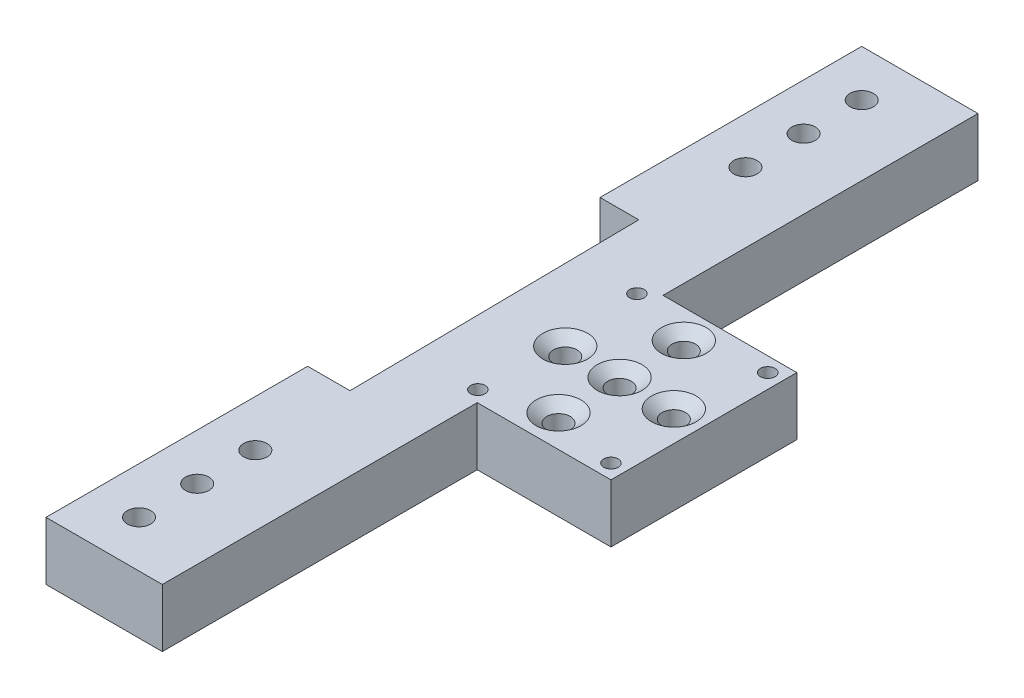
SolidWorks part; units mm, degrees
ref_plane "Front" through (0, 0, 0) normal (0, 0, 1) x (1, 0, 0)
ref_plane "Top" through (0, 0, 0) normal (0, 1, 0) x (1, 0, 0)
ref_plane "Right" through (0, 0, 0) normal (1, 0, 0) x (0, 0, -1)
sketch "Sketch1" plane through (0, 0, 0) normal (0, 1, 0) x (1, 0, 0)
  line L0 (24.6163, 0) -> (53.8263, 0)
  line L1 (53.8263, 0) -> (53.8263, 40.5892)
  line L2 (53.8263, 40.5892) -> (24.6163, 40.5892)
  line L3 (24.6163, 40.5892) -> (24.6163, 109.3724)
  line L4 (24.6163, 0) -> (24.6163, -68.7832)
  line L5 (24.6163, 109.3724) -> (-0.7837, 109.3724)
  line L6 (24.6163, -68.7832) -> (-0.7837, -68.7832)
  line L7 (-0.7837, 109.3724) -> (-0.7837, 52.2224)
  line L8 (-0.7837, -68.7832) -> (-0.7837, -11.6332)
  line L9 (-0.7837, -11.6332) -> (8.4582, -11.6332)
  line L10 (-0.7837, 52.2224) -> (7.6745, 52.2224)
  line L11 (7.6745, 52.2224) -> (8.4582, -11.6332)
extrude "Boss-Extrude1" add sketch "Sketch1" along normal blind 12.7
sketch "Sketch2" plane through (0, 12.7, 0) normal (0, 1, 0) x (1, 0, 0)
  line L0 (-0.7837, -68.7832) -> (-0.7837, -58.6232)
  line L1 (53.8263, 37.4142) -> (50.6513, 37.4142)
  line L2 (-0.7837, -11.6332) -> (-0.7837, -68.7832) construction
  line L3 (24.6163, 40.5892) -> (24.6163, 38.0492)
  line L4 (-0.7837, -58.6232) -> (9.3763, -58.6232)
  line L5 (-0.7837, 109.3724) -> (9.3763, 109.3724)
  line L6 (24.6163, 109.3724) -> (-0.7837, 109.3724) construction
  line L7 (9.3763, 109.3724) -> (9.3763, 99.2124)
  line L8 (53.8263, 20.2946) -> (35.4113, 20.2946)
  line L9 (53.8263, 0) -> (53.8263, 40.5892) construction
  line L10 (53.8263, 0) -> (53.8263, 3.175)
  line L11 (53.8263, 3.175) -> (50.6513, 3.175)
  line L12 (53.8263, 40.5892) -> (53.8263, 37.4142)
  line L13 (24.6163, 38.0492) -> (21.4413, 38.0492)
  line L14 (24.6163, 0) -> (24.6163, 2.54)
  line L15 (24.6163, 2.54) -> (22.2142, 2.54)
hole_wizard "1/4-20 Tapped Hole1" positions "Sketch11" profile "Sketch12" tap size "1/4-20" standard "ANSI Inch" end condition up to next
sketch "Sketch11" plane through (0, 12.7, 0) normal (0, 1, 0) x (1, 0, 0)
  point P0 (9.3763, 99.2124)
sketch "Sketch12" plane through (9.3763, 12.7, -99.2124) normal (1, 0, 0) x (0, 0, 1)
  line L0 (0, 0) -> (0, 12.7)
  line L1 (0, 12.7) -> (2.5527, 12.7)
  line L2 (2.5527, 12.7) -> (2.5527, 0)
  line L5 (2.5527, 0) -> (0, 0)
  line L11 (0, -6.35) -> (0, 107.95) construction
  dimension "Thread Major Dia." = 5.1054
  dimension "Thru Tap Drill Depth" = 12.7
hole_wizard "1/4-20 Tapped Hole2" positions "Sketch13" profile "Sketch14" tap size "1/4-20" standard "ANSI Inch" end condition up to next
sketch "Sketch13" plane through (0, 12.7, 0) normal (0, 1, 0) x (1, 0, 0)
  point P0 (9.3763, -58.6232)
sketch "Sketch14" plane through (9.3763, 12.7, 58.6232) normal (1, 0, 0) x (0, 0, 1)
  line L0 (0, 0) -> (0, 12.7)
  line L1 (0, 12.7) -> (2.5527, 12.7)
  line L2 (2.5527, 12.7) -> (2.5527, 0)
  line L5 (2.5527, 0) -> (0, 0)
  line L11 (0, -6.35) -> (0, 107.95) construction
  dimension "Thread Major Dia." = 5.1054
  dimension "Thru Tap Drill Depth" = 12.7
pattern_linear "LPattern1" count 3 spacing 12.7 along (0, 0, 1) of "1/4-20 Tapped Hole1"
pattern_linear "LPattern2" count 3 spacing 12.7 along (0, 0, -1) of "1/4-20 Tapped Hole2"
hole_wizard "CSK for #10 Flat Head Machine Screw (100)2" positions "Sketch20" profile "Sketch21" countersink size "#10" standard "ANSI Inch" end condition up to next
sketch "Sketch20" plane through (0, 12.7, 0) normal (0, 1, 0) x (1, 0, 0)
  point P0 (35.4113, 20.2946)
  point P3 (35.4113, 34.3262)
  point P5 (35.4113, 6.9607)
sketch "Sketch21" plane through (35.4113, 12.7, -20.2946) normal (1, 0, 0) x (0, 0, 1)
  line L0 (0, 0) -> (0, 12.7)
  line L1 (0, 12.7) -> (2.5527, 12.7)
  line L2 (2.5527, 12.7) -> (2.5527, 1.9608)
  line L3 (2.5527, 1.9608) -> (4.8895, 0)
  line L5 (4.8895, 0) -> (0, 0)
  line L6 (-2.5527, 1.9608) -> (-4.8895, 0) construction
  line L11 (0, -6.35) -> (0, 107.95) construction
  dimension "Thru Hole Dia." = 5.1054
  dimension "Thru Hole Depth" = 12.7
  dimension "Near C'Sink Dia." = 9.779
  dimension "Near C'Sink Angle" = 100
hole_wizard "1/8 (0.125) Diameter Hole1" positions "Sketch27" profile "Sketch28" hole size "1/8" standard "ANSI Inch" end condition up to next
sketch "Sketch27" plane through (0, 12.7, 0) normal (0, 1, 0) x (1, 0, 0)
  point P0 (21.4413, 38.0492)
  point P3 (22.2142, 2.54)
  point P6 (50.6513, 3.175)
  point P9 (50.6513, 37.4142)
sketch "Sketch28" plane through (21.4413, 12.7, -38.0492) normal (1, 0, 0) x (0, 0, 1)
  line L0 (0, 0) -> (0, 12.7)
  line L1 (0, 12.7) -> (1.5875, 12.7)
  line L2 (1.5875, 12.7) -> (1.5875, 0)
  line L5 (1.5875, 0) -> (0, 0)
  line L11 (0, -6.35) -> (0, 107.95) construction
  dimension "Thru Hole Dia." = 3.175
  dimension "Thru Hole Depth" = 12.7
hole_wizard "CSK for #10 Flat Head Machine Screw (100)3" positions "Sketch29" profile "Sketch30" countersink size "#10" standard "ANSI Inch" end condition up to next
sketch "Sketch29" plane through (0, 12.7, 0) normal (0, 1, 0) x (1, 0, 0)
  line L0 (53.8263, 20.2946) -> (35.4113, 20.2946) construction
  point P0 (47.2605, 20.2946)
  point P4 (23.5448, 20.2946)
sketch "Sketch30" plane through (47.2605, 12.7, -20.2946) normal (1, 0, 0) x (0, 0, 1)
  line L0 (0, 0) -> (0, 12.7)
  line L1 (0, 12.7) -> (2.5527, 12.7)
  line L2 (2.5527, 12.7) -> (2.5527, 1.9608)
  line L3 (2.5527, 1.9608) -> (4.8895, 0)
  line L5 (4.8895, 0) -> (0, 0)
  line L6 (-2.5527, 1.9608) -> (-4.8895, 0) construction
  line L11 (0, -6.35) -> (0, 107.95) construction
  dimension "Thru Hole Dia." = 5.1054
  dimension "Thru Hole Depth" = 12.7
  dimension "Near C'Sink Dia." = 9.779
  dimension "Near C'Sink Angle" = 100
